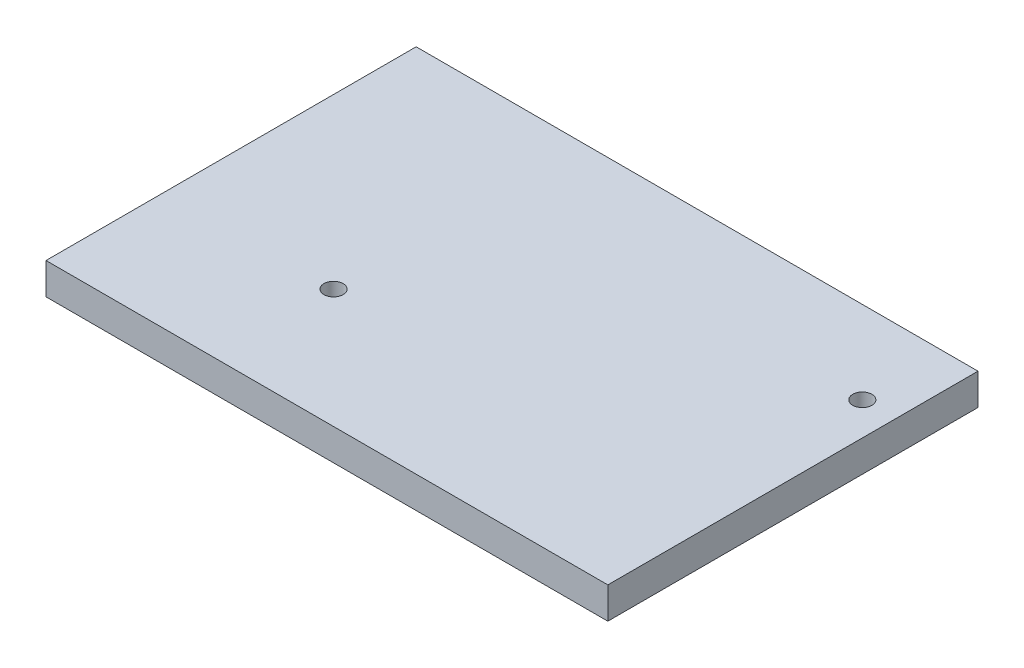
SolidWorks part; units mm, degrees
ref_plane "Front" through (0, 0, 0) normal (0, 0, 1) x (1, 0, 0)
ref_plane "Top" through (0, 0, 0) normal (0, 1, 0) x (1, 0, 0)
ref_plane "Right" through (0, 0, 0) normal (1, 0, 0) x (0, 0, -1)
sketch "Sketch1" plane through (0, 0, 0) normal (0, 1, 0) x (1, 0, 0)
  line L1 (-42.5, -28) -> (42.5, -28)
  line L2 (-42.5, -28) -> (-42.5, 28)
  line L3 (-42.5, 28) -> (42.5, 28)
  line L4 (42.5, -28) -> (42.5, 28)
  circle A0 centre (37.5, 15.5) radius 1.45 construction
  circle A1 centre (-17, -10) radius 1.45 construction
extrude "Boss-Extrude1" add sketch "Sketch1" along normal blind 4.7625
sketch "Sketch2" plane through (0, 0, 0) normal (0, -1, 0) x (1, 0, 0)
  point P0 (-17, 10)
  point P1 (37.5, -15.5)
hole_wizard "CSK for M2.5 Flat Head Machine Screw1" positions "3DSketch1" profile "Sketch3" countersink size "M2.5" standard "ANSI Metric" end condition through all
sketch3d "3DSketch1"
  point P0 (-17, 0, 10)
  point P2 (37.5, 0, -15.5)
sketch "Sketch3" plane through (-17, 0, 10) normal (1, 0, 0) x (0, 0, -1)
  line L0 (0, 0) -> (0, 4.7625)
  line L1 (0, 4.7625) -> (1.45, 4.7625)
  line L2 (1.45, 4.7625) -> (1.45, 2.3)
  line L3 (1.45, 2.3) -> (3.75, 0)
  line L5 (3.75, 0) -> (0, 0)
  line L6 (-1.45, 2.3) -> (-3.75, 0) construction
  line L11 (0, -6.35) -> (0, 107.95) construction
  dimension "Thru Hole Dia." = 2.9
  dimension "Thru Hole Depth" = 4.7625
  dimension "Near C'Sink Dia." = 7.5
  dimension "Near C'Sink Angle" = 90
